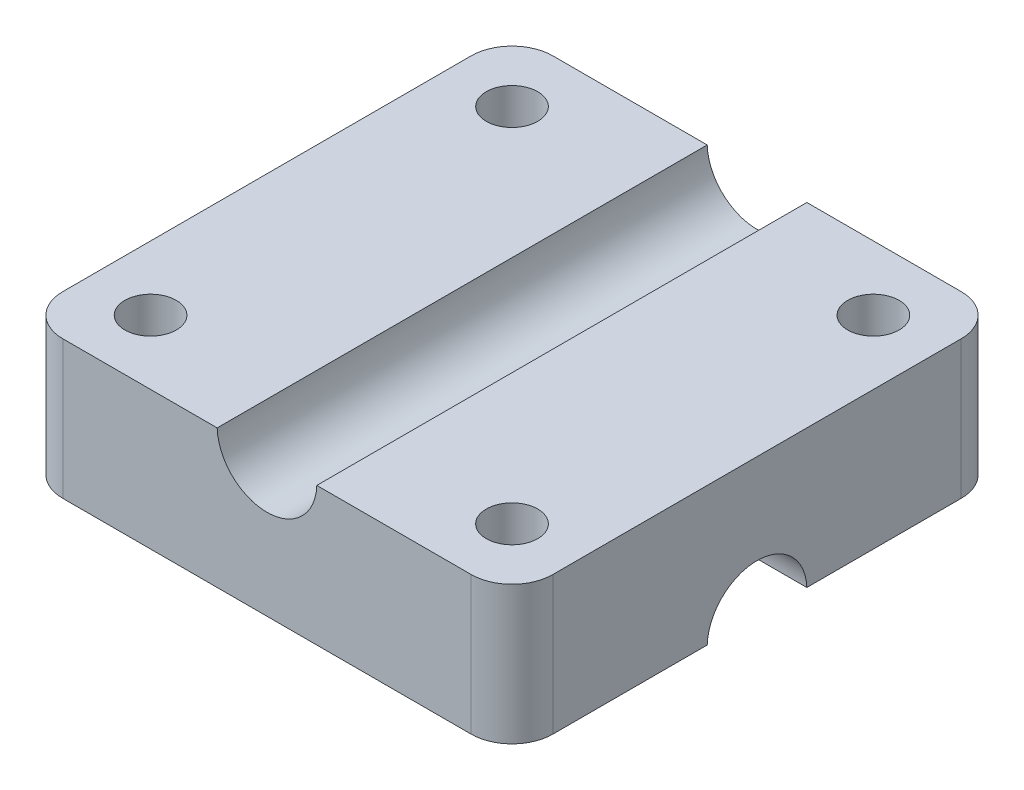
SolidWorks part; units mm, degrees
ref_plane "前视基准面" through (0, 0, 0) normal (0, 0, 1) x (1, 0, 0)
ref_plane "上视基准面" through (0, 0, 0) normal (0, 1, 0) x (1, 0, 0)
ref_plane "右视基准面" through (0, 0, 0) normal (1, 0, 0) x (0, 0, -1)
sketch "草图2" plane through (0, 0, 0) normal (0, 1, 0) x (1, 0, 0)
  line L1 (-15.24, -15.24) -> (15.24, -15.24)
  line L2 (-15.24, -15.24) -> (-15.24, 15.24)
  line L3 (-15.24, 15.24) -> (15.24, 15.24)
  line L4 (15.24, -15.24) -> (15.24, 15.24)
  line L5 (-15.24, -15.24) -> (15.24, 15.24) construction
  line L6 (-15.24, 15.24) -> (15.24, -15.24) construction
  point P0 (0, 0)
  dimension "D1" = 30.48
  dimension "D2" = 30.48
extrude "凸台-拉伸1" add sketch "草图2" along normal blind 8.6
sketch "草图3" plane through (0, 0, 15.24) normal (0, 0, 1) x (1, 0, 0)
  line L0 (-15.24, 8.6) -> (15.24, 8.6) construction
  line L3 (0, 4.3) -> (0, 10.2423) construction
  circle A0 centre (0, 8.7) radius 3.1
  point P0 (0, 9.4115)
  dimension "D2" = 6.2
  dimension "D1" = 0.1
extrude "切除-拉伸1" cut sketch "草图3" against normal up to surface (30.48 mm away) up to face at (0, 4.3, -15.24)
sketch "草图4" plane through (15.24, 0, 0) normal (1, 0, 0) x (0, 0, -1)
  line L0 (-15.24, 0) -> (15.24, 0) construction
  line L3 (0, 8.6) -> (0, 0) construction
  circle A0 centre (0, -0.1) radius 3.1
  dimension "D1" = 6.2
  dimension "D2" = 0.1
extrude "切除-拉伸2" cut sketch "草图4" against normal up to surface (30.48 mm away) up to face at (-15.24, 4.3, 0)
fillet "圆角1" [suppressed] radius 2.54
sketch "草图5" plane through (0, 0, 0) normal (0, -1, 0) x (1, 0, 0)
  line L0 (-15.24, 15.24) -> (0, 0) construction
  line L1 (-15.24, 3.0984) -> (-15.24, 15.24) construction
  circle A0 centre (-11.24, 11.24) radius 1.6
  circle A1 centre (11.24, 11.24) radius 1.6
  circle A2 centre (11.24, -11.24) radius 1.6
  circle A3 centre (-11.24, -11.24) radius 1.6
  point P17 (0, 0)
  dimension "D1" = 3.2
  dimension "D2" = 4
  dimension "D3" = 4
extrude "切除-拉伸3" cut sketch "草图5" against normal through all
fillet "圆角2" radius 2.54 4 edges at (15.24, 4.3, 15.24) (15.24, 4.3, -15.24) (-15.24, 4.3, -15.24) (-15.24, 4.3, 15.24)
